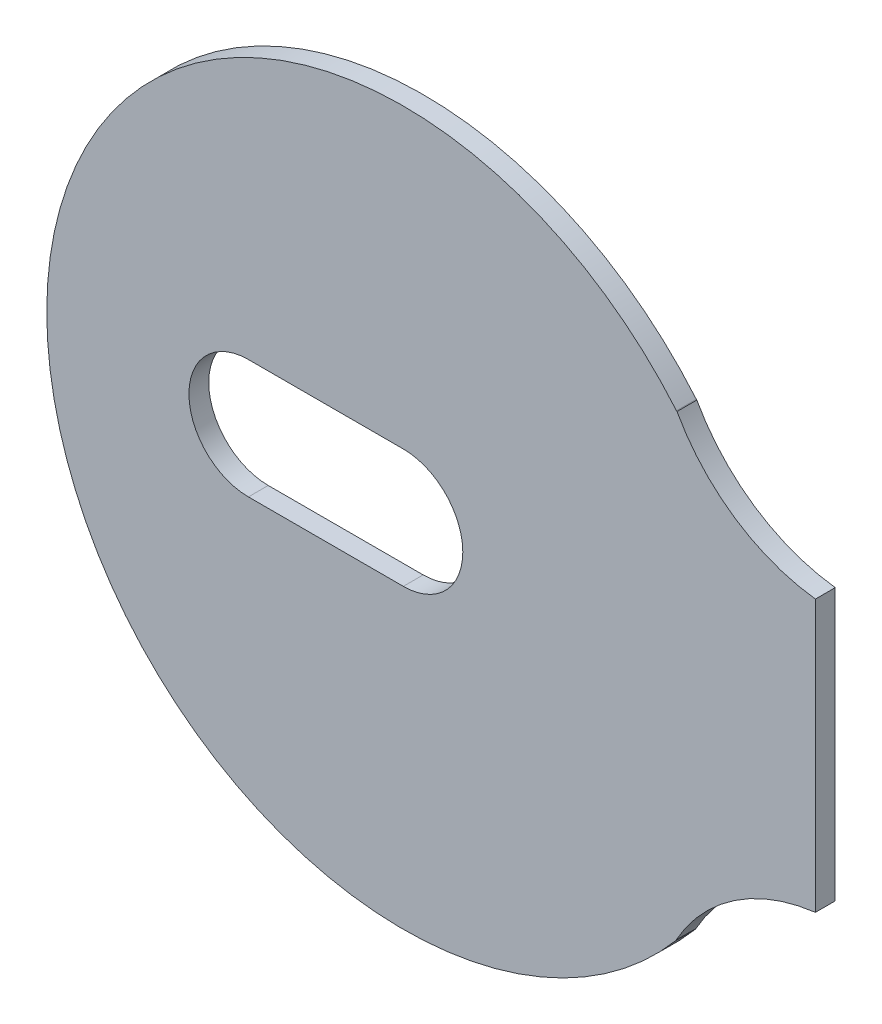
SolidWorks part; units mm, degrees
ref_plane "前视基准面" through (0, 0, 0) normal (0, 0, 1) x (1, 0, 0)
ref_plane "上视基准面" through (0, 0, 0) normal (0, 1, 0) x (1, 0, 0)
ref_plane "右视基准面" through (0, 0, 0) normal (1, 0, 0) x (0, 0, -1)
sketch "草图1" plane through (0, 0, 0) normal (0, 0, 1) x (1, 0, 0)
  line L6 (-7.8156, 3) -> (0, 3)
  line L7 (0, -3) -> (-7.8156, -3)
  line L8 (13.7562, -11.5893) -> (13.7557, -11.5762)
  line L9 (20.7873, -6.85) -> (20.7873, 6.8387)
  line L10 (13.8051, 11.5407) -> (13.7808, 11.5603)
  line L11 (13.7808, 11.5603) -> (13.7791, 11.562)
  arc A5 (0, -3) -> (0, 3) centre (0, 0) ccw
  arc A6 (20.7873, -6.85) -> (13.7557, -11.5762) centre (21.9239, -16.1348) ccw
  arc A7 (13.8051, 11.5407) -> (20.7873, 6.8387) centre (21.8619, 15.9695) ccw
  arc A8 (13.7791, 11.562) -> (13.7562, -11.5893) centre (0, 0) ccw
  arc A9 (-7.8156, 3) -> (-7.8156, -3) centre (-7.816, 0) ccw
extrude "凸台-拉伸1" add sketch "草图1" along normal blind 1
